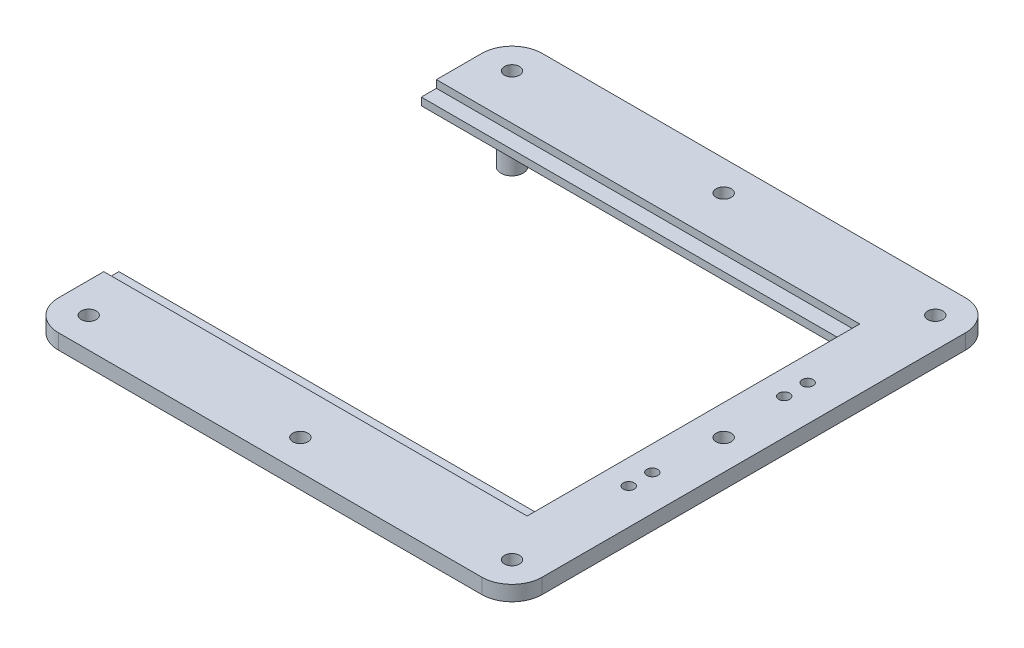
SolidWorks part; units mm, degrees
ref_plane "Front Plane" through (0, 0, 0) normal (0, 0, 1) x (1, 0, 0)
ref_plane "Top Plane" through (0, 0, 0) normal (0, 1, 0) x (1, 0, 0)
ref_plane "Right Plane" through (0, 0, 0) normal (1, 0, 0) x (0, 0, -1)
sketch "Sketch1" plane through (0, 0, 0) normal (0, 1, 0) x (1, 0, 0)
  line L0 (0, 0) -> (0, 25.4)
  line L1 (12.7, 38.1) -> (190.5, 38.1)
  line L2 (203.2, 25.4) -> (203.2, -152.4)
  line L3 (190.5, -165.1) -> (12.7, -165.1)
  line L4 (0, -152.4) -> (0, -127)
  line L5 (0, -127) -> (177.8, -127)
  line L6 (177.8, -127) -> (177.8, 0)
  line L7 (177.8, 0) -> (0, 0)
  arc A0 (12.7, -165.1) -> (0, -152.4) centre (12.7, -152.4) cw
  arc A1 (203.2, -152.4) -> (190.5, -165.1) centre (190.5, -152.4) cw
  arc A2 (190.5, 38.1) -> (203.2, 25.4) centre (190.5, 25.4) cw
  arc A3 (0, 25.4) -> (12.7, 38.1) centre (12.7, 25.4) cw
  point P13 (203.2, -165.1)
  point P16 (203.2, 38.1)
  point P19 (0, 38.1)
  dimension "D6" = 12.7
  dimension "D1" = 203.2
  dimension "D2" = 38.1
  dimension "D3" = 203.2
  dimension "D4" = 177.8
  dimension "D5" = 127
extrude "Boss-Extrude2" add sketch "Sketch1" along normal blind 6.35
sketch "Sketch2" plane through (0, 6.35, 0) normal (0, 1, 0) x (1, 0, 0)
  circle A0 centre (12.7, 25.4) radius 3.175
  circle A1 centre (190.5, 25.4) radius 3.175
  circle A2 centre (190.5, -152.4) radius 3.175
  circle A3 centre (12.7, -152.4) radius 3.175
  arc A4 (12.7, 38.1) -> (0, 25.4) centre (12.7, 25.4) ccw construction
  dimension "D1" = 6.35
extrude "Cut-Extrude1" cut sketch "Sketch2" against normal through all
sketch "Sketch5" plane through (0, 0, 0) normal (0, -1, 0) x (1, 0, 0)
  line L0 (0, 127) -> (0, 152.4) construction
  line L1 (12.7, 165.1) -> (190.5, 165.1) construction
  line L2 (203.2, 152.4) -> (203.2, -25.4) construction
  line L4 (203.2, 63.5) -> (0, 63.5) construction
  circle A0 centre (28.575, 136.525) radius 4.6625
  circle A1 centre (174.625, 136.525) radius 4.6625
  circle A4 centre (174.625, -9.525) radius 4.6625
  circle A5 centre (28.575, -9.525) radius 4.6625
  dimension "D1" = 28.575
  dimension "D2" = 28.575
  dimension "D3" = 9.325
  dimension "D4" = 28.575
  dimension "D5" = 28.575
extrude "Boss-Extrude3" add sketch "Sketch5" along normal blind 12.7
sketch "Sketch6" plane through (0, 6.35, 0) normal (0, 1, 0) x (1, 0, 0)
  line L0 (0, -127) -> (0, -152.4) construction
  line L1 (177.8, -127) -> (0, -127)
  line L2 (177.8, -127) -> (177.8, -133.35)
  line L3 (177.8, -133.35) -> (0, -133.35)
  line L4 (0, -127) -> (0, -133.35)
  line L5 (203.2, -63.5) -> (0, -63.5) construction
  line L6 (203.2, -152.4) -> (203.2, 25.4) construction
  line L7 (0, 0) -> (0, 6.35)
  line L8 (177.8, 6.35) -> (0, 6.35)
  line L9 (177.8, 0) -> (177.8, 6.35)
  line L10 (177.8, 0) -> (0, 0)
  dimension "D1" = 6.35
extrude "Cut-Extrude2" cut sketch "Sketch6" against normal blind 3.175
sketch "Sketch7" plane through (0, 6.35, 0) normal (0, 1, 0) x (1, 0, 0)
  line L0 (188.214, -28.194) -> (188.214, -33.528) construction
  line L1 (188.214, -38.1) -> (188.214, -88.9) construction
  line L2 (188.214, -93.472) -> (188.214, -98.806) construction
  line L3 (188.214, -23.622) -> (188.214, 38.1) construction
  line L4 (190.5, 38.1) -> (12.7, 38.1) construction
  line L5 (188.214, -103.378) -> (188.214, -165.1) construction
  line L6 (12.7, -165.1) -> (190.5, -165.1) construction
  line L7 (185.928, -25.908) -> (177.8, -25.908) construction
  line L8 (177.8, 6.35) -> (177.8, -133.35) construction
  circle A0 centre (188.214, -101.092) radius 2.286
  circle A1 centre (188.214, -91.186) radius 2.286
  circle A2 centre (188.214, -35.814) radius 2.286
  circle A3 centre (188.214, -25.908) radius 2.286
  dimension "D1" = 4.572
  dimension "D2" = 5.334
  dimension "D3" = 5.334
  dimension "D4" = 50.8
  dimension "D5" = 8.128
extrude "Cut-Extrude3" cut sketch "Sketch7" against normal blind 12.7
sketch "Sketch8" plane through (0, 6.35, 0) normal (0, 1, 0) x (1, 0, 0)
  line L0 (12.7, -152.4) -> (190.5, 25.4) construction
  line L1 (12.7, 25.4) -> (190.5, -152.4) construction
  line L2 (190.5, 38.1) -> (12.7, 38.1) construction
  circle A0 centre (101.6, 25.4) radius 3.175
  circle A1 centre (190.5, -63.5) radius 3.175
  circle A2 centre (101.6, -152.4) radius 3.175
  circle A4 centre (12.7, -63.5) radius 3.175 [skipped]
  point P12 (101.6, 38.1)
  point P13 (101.6, -63.5)
  dimension "D3" = 6.35
  dimension "D2" = 12.7
  dimension "D1" = 4
extrude "Cut-Extrude4" cut sketch "Sketch8" against normal through all
